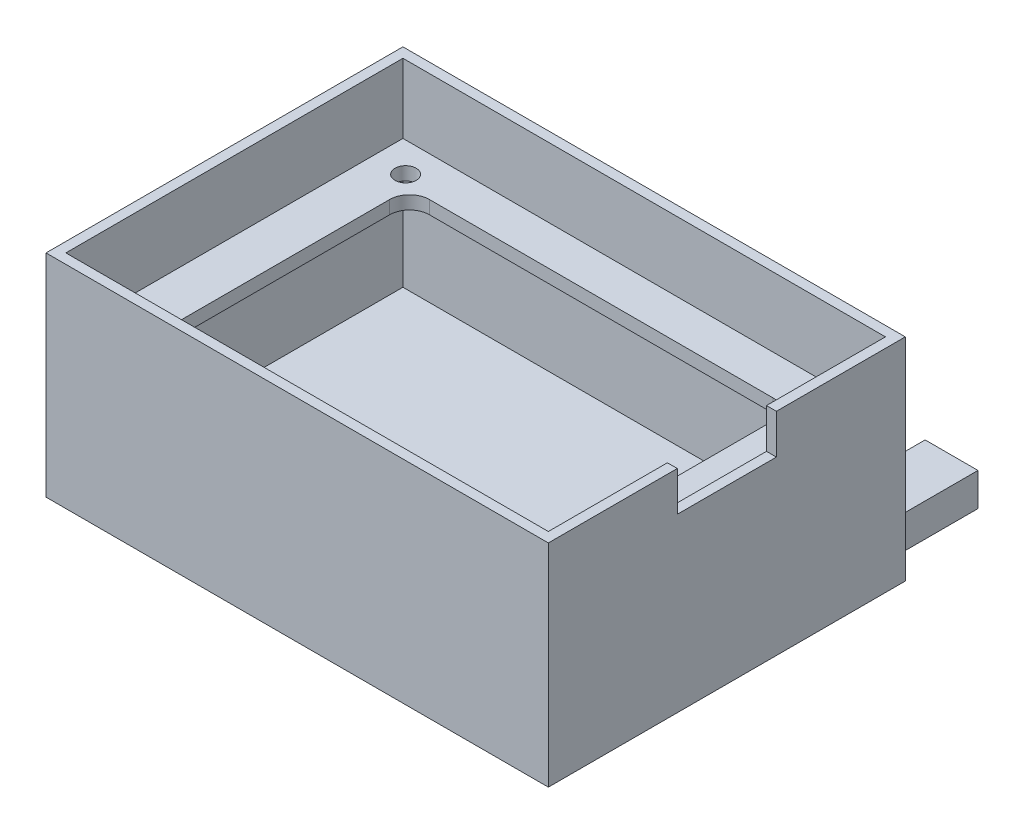
SolidWorks part; units mm, degrees
ref_plane "Front Plane" through (0, 0, 0) normal (0, 0, 1) x (1, 0, 0)
ref_plane "Top Plane" through (0, 0, 0) normal (0, 1, 0) x (1, 0, 0)
ref_plane "Right Plane" through (0, 0, 0) normal (1, 0, 0) x (0, 0, -1)
sketch "Enclosure Shell Sketch" plane through (0, 0, 0) normal (0, 1, 0) x (1, 0, 0)
  line L1 (38, 27) -> (-38, 27)
  line L2 (38, 27) -> (38, -27)
  line L3 (38, -27) -> (-38, -27)
  line L4 (-38, 27) -> (-38, -27)
  line L5 (38, 27) -> (-38, -27) construction
  line L6 (38, -27) -> (-38, 27) construction
  point P0 (0, 0)
  dimension "D1" = 76
  dimension "D2" = 54
extrude "Enclosure Shell Feature" add sketch "Enclosure Shell Sketch" along normal blind 32
sketch "Enclosure Gap Sketch" plane through (0, 32, 0) normal (0, 1, 0) x (1, 0, 0)
  line L1 (-36.5, 25.5) -> (36.5, 25.5)
  line L2 (-36.5, 25.5) -> (-36.5, -25.5)
  line L3 (-36.5, -25.5) -> (36.5, -25.5)
  line L4 (36.5, 25.5) -> (36.5, -25.5)
  line L5 (-36.5, 25.5) -> (36.5, -25.5) construction
  line L6 (-36.5, -25.5) -> (36.5, 25.5) construction
  point P0 (0, 0)
  dimension "D1" = 51
  dimension "D2" = 73
extrude "Enclosure Gap Feature" cut sketch "Enclosure Gap Sketch" against normal blind 30
sketch "Screw Shell Sketch" plane through (0, 2, 0) normal (0, 1, 0) x (1, 0, 0)
  line L0 (-38, 27) -> (-38, -27) construction
  line L6 (38, -27) -> (38, 27) construction
  line L7 (38, 27) -> (-38, 27) construction
  line L8 (-38, -27) -> (38, -27) construction
  circle A0 centre (-31.0885, 20.5) radius 2.5
  circle A1 centre (-31.1, -20.5) radius 2.5
  circle A2 centre (31.1, 20.5) radius 2.5
  circle A3 centre (31.1, -20.5) radius 2.5
  point P14 (0, 0)
  dimension "D1" = 6.5
  dimension "D3" = 6.5
  dimension "D5" = 6.9
  dimension "D7" = 6.9115
  dimension "D2" = 6.9
  dimension "D4" = 6.5
  dimension "D6" = 6.5
  dimension "D8" = 6.9
extrude "Screw Shell Feature" add sketch "Screw Shell Sketch" along normal blind 8
sketch "Battery Cut Sketch" plane through (38, 0, 0) normal (-1, 0, 0) x (0, 0, 1)
  line L0 (0, 32) -> (7.4925, 32)
  line L1 (-27, 32) -> (27, 32) construction
  line L2 (7.4925, 32) -> (7.4925, 26)
  line L3 (7.4925, 26) -> (-7.5, 26)
  line L4 (-7.5, 26) -> (-7.5, 32)
  line L5 (-7.5, 32) -> (0, 32)
  dimension "D1" = 6
  dimension "D2" = 6
extrude "Battery Cut" cut sketch "Battery Cut Sketch" along normal up to next and the other way through all
sketch "Camera Cord Hole Sketch" plane through (0, 2, 0) normal (0, 1, 0) x (1, 0, 0)
  line L1 (-27.5, -3.5) -> (-7.5, -3.5)
  line L2 (-27.5, -3.5) -> (-27.5, -15.5)
  line L3 (-27.5, -15.5) -> (-7.5, -15.5)
  line L4 (-7.5, -3.5) -> (-7.5, -15.5)
  line L5 (-27.5, -3.5) -> (-7.5, -15.5) construction
  line L6 (-27.5, -15.5) -> (-7.5, -3.5) construction
  line L10 (-36.5, 25.5) -> (-36.5, -25.5) construction
  line L11 (-36.5, -25.5) -> (36.5, -25.5) construction
  point P0 (-17.5, -9.5)
  dimension "D1" = 12
  dimension "D2" = 20
  dimension "D3" = 19
  dimension "D4" = 10
extrude "Camera Cord Hole" cut sketch "Camera Cord Hole Sketch" against normal through all
sketch "Tab Feature Sketch" plane through (0, 0, -27) normal (0, 0, -1) x (-1, 0, 0)
  line L0 (-38, 0) -> (38, 0) construction
  line L1 (-34, 5) -> (-26, 5)
  line L2 (-34, 5) -> (-34, 0)
  line L3 (-34, 0) -> (-26, 0)
  line L4 (-26, 5) -> (-26, 0)
  line L5 (-34, 5) -> (-26, 0) construction
  line L6 (-34, 0) -> (-26, 5) construction
  line L7 (-38, 32) -> (-38, 0) construction
  line L13 (38, 32) -> (38, 0) construction
  line L14 (26, 5) -> (34, 5)
  line L15 (26, 5) -> (26, 0)
  line L16 (26, 0) -> (34, 0)
  line L17 (34, 5) -> (34, 0)
  line L18 (26, 5) -> (34, 0) construction
  line L19 (26, 0) -> (34, 5) construction
  point P0 (-30, 2.5)
  point P9 (30, 2.5)
  dimension "D1" = 8
  dimension "D2" = 5
  dimension "D3" = 0
  dimension "D4" = 4
  dimension "D5" = 4
  dimension "D6" = 5
  dimension "D7" = 8
extrude "Tab Feature" add sketch "Tab Feature Sketch" along normal blind 15
sketch "Sketch1" plane through (0, 0, 0) normal (0, -1, 0) x (-1, 0, 0)
  line L0 (38, 27) -> (38, -27) construction
  line L1 (36, -25) -> (-36, -25)
  line L2 (36, -25) -> (36, 25)
  line L3 (36, 25) -> (-36, 25)
  line L4 (-36, -25) -> (-36, 25)
  line L5 (36, -25) -> (-36, 25) construction
  line L6 (36, 25) -> (-36, -25) construction
  point P0 (0, 0)
  dimension "D1" = 50
  dimension "D2" = 72
  dimension "D3" = 2
extrude "Boss-Extrude2" add sketch "Sketch1" against normal blind 20 from offset 2 offset against normal yes
sketch "Sketch2" plane through (0, 0, 0) normal (0, -1, 0) x (-1, 0, 0)
  line L1 (36, -25) -> (-36, -25)
  line L2 (36, -25) -> (36, 25)
  line L3 (36, 25) -> (-36, 25)
  line L4 (-36, -25) -> (-36, 25)
  line L5 (36, -25) -> (-36, 25) construction
  line L6 (36, 25) -> (-36, -25) construction
  point P0 (0, 0)
  dimension "D1" = 50
  dimension "D2" = 72
extrude "Cut-Extrude1" cut sketch "Sketch2" against normal blind 18 from offset 2 offset against normal yes
sketch "Sketch4" plane through (0, 22, 0) normal (0, 1, 0) x (1, 0, 0)
  line L1 (-29, 19) -> (29, 19)
  line L2 (-29, 19) -> (-29, -19)
  line L3 (-29, -19) -> (29, -19)
  line L4 (29, 19) -> (29, -19)
  line L5 (-29, 19) -> (29, -19) construction
  line L6 (-29, -19) -> (29, 19) construction
  point P0 (0, 0)
  dimension "D1" = 38
  dimension "D2" = 58
extrude "Cut-Extrude3" cut sketch "Sketch4" against normal blind 2
sketch "Sketch5" plane through (0, 22, 0) normal (0, 1, 0) x (1, 0, 0)
  line L0 (38, 27) -> (-38, 27) construction
  line L1 (-38, 27) -> (-38, -27) construction
  line L2 (38, 7.5) -> (38, 27) construction
  line L3 (38, -27) -> (38, -7.4925) construction
  line L4 (-38, -27) -> (38, -27) construction
  circle A0 centre (-31.1, 20.5) radius 1.6
  circle A1 centre (31.1, 20.5) radius 1.6
  circle A2 centre (31.1, -20.5) radius 1.6
  circle A3 centre (-31.1, -20.5) radius 1.6
  dimension "D3" = 6.5
  dimension "D5" = 6.9
  dimension "D7" = 6.5
  dimension "D1" = 6.5
  dimension "D2" = 6.9
  dimension "D4" = 6.9
  dimension "D6" = 6.5
  dimension "D8" = 6.9
extrude "Cut-Extrude4" cut sketch "Sketch5" against normal blind 10
fillet "Fillet1" radius 3 1 edges at (-29, 21, -19)
fillet "Fillet3" radius 3 1 edges at (29, 21, -19)
fillet "Fillet4" radius 3 1 edges at (29, 21, 19)
fillet "Fillet5" radius 3 1 edges at (-29, 21, 19)
